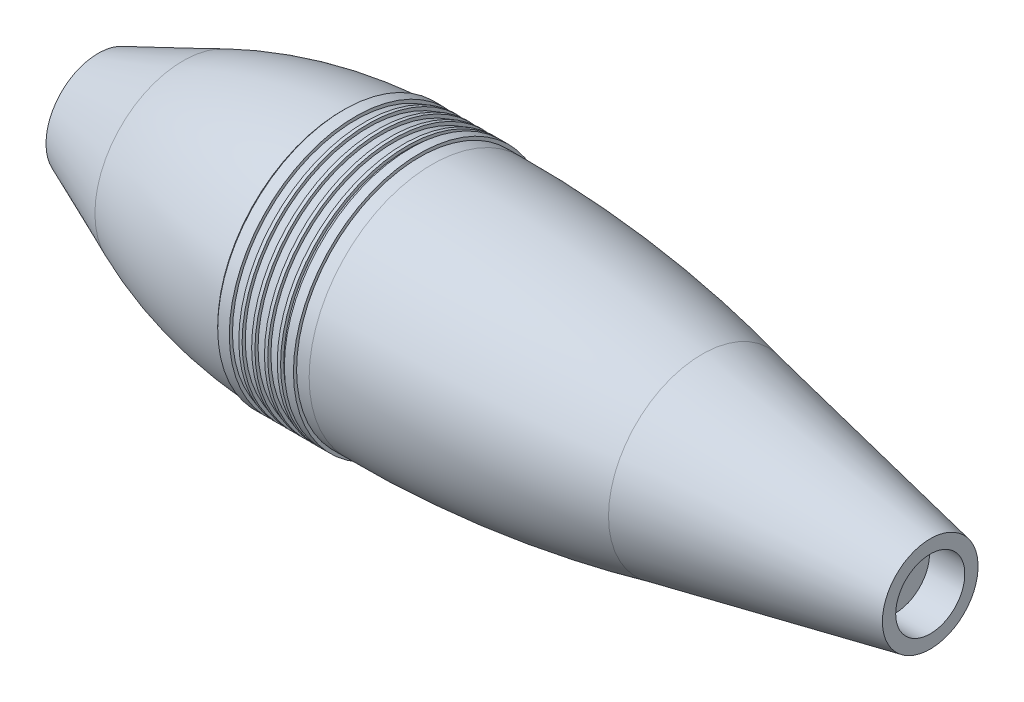
SolidWorks part; units mm, degrees
material "AISI 1045 Steel, cold drawn"
ref_plane "Front Plane" through (0, 0, 0) normal (0, 0, 1) x (1, 0, 0)
ref_plane "Top Plane" through (0, 0, 0) normal (0, 1, 0) x (1, 0, 0)
ref_plane "Right Plane" through (0, 0, 0) normal (1, 0, 0) x (0, 0, -1)
sketch "Sketch1" plane through (0, 0, 0) normal (0, 0, 1) x (1, 0, 0)
  line L0 (-198.645, 0) -> (198.645, 0) construction
  line L1 (-198.645, 14.5) -> (-198.645, 0) construction
  line L2 (-198.645, 0) -> (-158.065, 0) construction
  line L3 (-158.065, 0) -> (-158.065, 42.12) construction
  line L4 (-198.645, 24.89) -> (-158.065, 42.12)
  line L5 (-158.065, 0) -> (-82.295, 0) construction
  line L6 (-82.295, 0) -> (-82.295, 59.27) construction
  line L7 (-75.755, 60.27) -> (-75.755, 58.765)
  line L8 (-75.755, 58.765) -> (-71.215, 60.27)
  line L9 (-81.295, 60.27) -> (-75.755, 60.27)
  line L10 (-71.215, 60.27) -> (-69.635, 60.27)
  line L11 (-69.635, 60.27) -> (-69.635, 58.765)
  line L12 (-63.515, 60.27) -> (-63.515, 58.765)
  line L13 (-65.095, 60.27) -> (-63.515, 60.27)
  line L14 (-69.635, 58.765) -> (-65.095, 60.27)
  line L15 (-57.395, 60.27) -> (-57.395, 58.765)
  line L16 (-58.975, 60.27) -> (-57.395, 60.27)
  line L17 (-63.515, 58.765) -> (-58.975, 60.27)
  line L18 (-51.275, 60.27) -> (-51.275, 58.765)
  line L19 (-52.855, 60.27) -> (-51.275, 60.27)
  line L20 (-57.395, 58.765) -> (-52.855, 60.27)
  line L21 (-51.275, 58.765) -> (-49.475, 60.27)
  line L22 (-49.475, 60.27) -> (-45.135, 60.27)
  line L23 (-45.135, 60.27) -> (-45.135, 58.765)
  line L24 (-45.135, 58.765) -> (-44.135, 58.765)
  line L25 (-44.135, 58.765) -> (-39.135, 58.765)
  line L26 (89.705, 0) -> (89.705, 44.67) construction
  line L28 (89.705, 44.67) -> (198.645, 22.84)
  line L29 (198.645, 16.5) -> (181.815, 16.5)
  line L30 (198.645, 22.84) -> (198.645, 16.5)
  line L32 (181.815, 16.5) -> (181.815, 0)
  line L33 (181.815, 0) -> (171.905, 0)
  line L34 (89.705, 0) -> (89.705, 36.22) construction
  line L35 (171.905, 0) -> (171.905, 8.6153)
  line L36 (-10.775, 0) -> (-10.775, 47.63) construction
  line L37 (-10.775, 47.63) -> (-79.995, 47.63)
  line L38 (-198.645, 24.89) -> (-198.645, 14.5)
  line L39 (-198.645, 14.5) -> (-182.645, 14.5)
  line L40 (-182.645, 14.5) -> (-182.645, 17.3451)
  line L41 (164.2378, 18.3394) -> (89.705, 36.22)
  arc A0 (-158.065, 42.12) -> (-82.295, 59.27) centre (-72.7911, -158.6729) cw
  arc A1 (-82.295, 59.27) -> (-81.295, 60.27) centre (-83.4906, 61.4656) ccw
  arc A2 (-39.135, 58.765) -> (89.705, 44.67) centre (-35.2543, -501.6616) cw
  arc A3 (-10.775, 47.63) -> (89.705, 36.22) centre (-30.7217, -576.1612) cw
  arc A4 (-181.5978, 19.2189) -> (-79.995, 47.63) centre (-81.1844, -143.9963) cw
  arc A5 (-181.5978, 19.2189) -> (-182.645, 17.3451) centre (-180.445, 17.3451) ccw
  arc A6 (164.2378, 18.3394) -> (171.905, 8.6153) centre (161.905, 8.6153) cw
  dimension "D7" = 218.15
  dimension "D10" = 1.58
  dimension "D19" = 560.44
  dimension "D27" = 624.11
  dimension "D32" = 191.63
  dimension "D33" = 4.4
  dimension "D34" = 10
  dimension "D37" = 2.5
  dimension "D1" = 397.29
  dimension "D2" = 40.58
  dimension "D3" = 24.89
  dimension "D4" = 42.12
  dimension "D5" = 75.77
  dimension "D6" = 59.27
  dimension "D8" = 58.765
  dimension "D9" = 4.54
  dimension "D11" = 5.54
  dimension "D12" = 4
  dimension "D13" = 1.8
  dimension "D14" = 4.34
  dimension "D15" = 1
  dimension "D16" = 5
  dimension "D17" = 44.67
  dimension "D18" = 108.94
  dimension "D20" = 22.84
  dimension "D21" = 16.5
  dimension "D22" = 16.83
  dimension "D23" = 9.91
  dimension "D24" = 36.22
  dimension "D25" = 47.63
  dimension "D26" = 100.48
  dimension "D28" = 69.22
  dimension "D29" = 14.5
  dimension "D30" = 19.2189
  dimension "D31" = 16
  dimension "D35" = 16.5
  dimension "D36" = 74.5328
  dimension "D38" = 1.505
revolve "Revolve7" add sketch "Sketch1" angle 360 about L0
